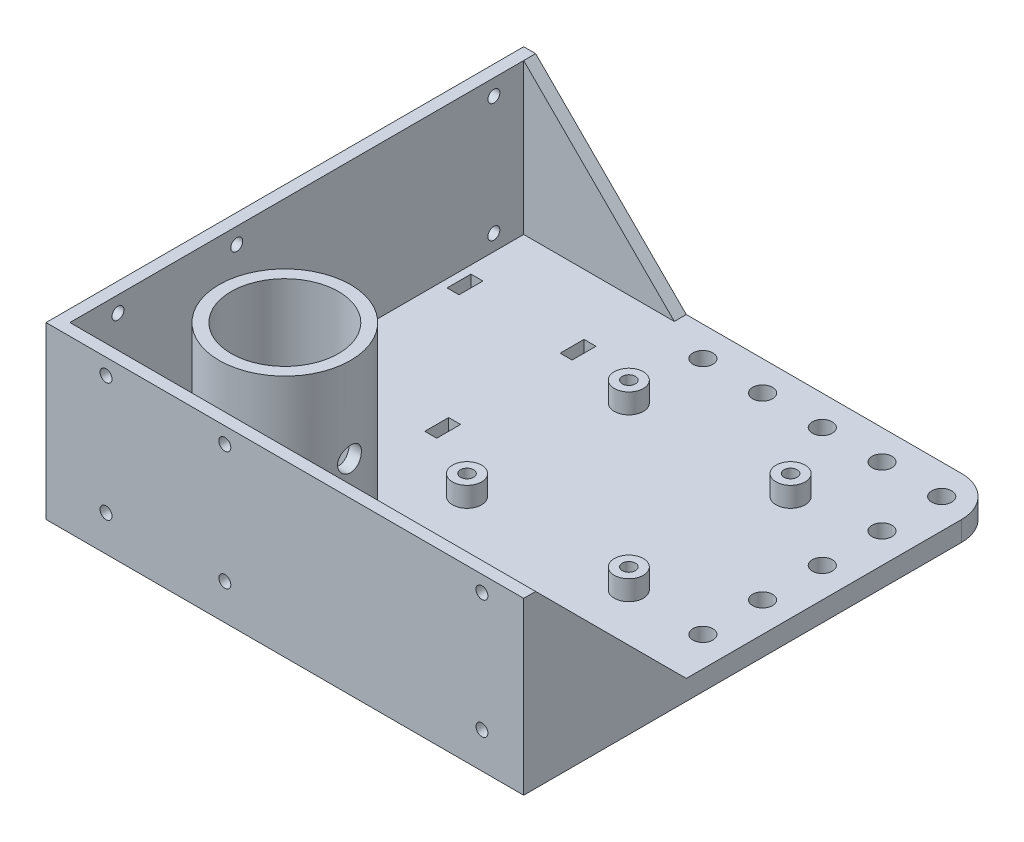
SolidWorks part; units mm, degrees
ref_plane "Front Plane" through (0, 0, 0) normal (0, 0, 1) x (1, 0, 0)
ref_plane "Top Plane" through (0, 0, 0) normal (0, 1, 0) x (1, 0, 0)
ref_plane "Right Plane" through (0, 0, 0) normal (1, 0, 0) x (0, 0, -1)
sketch "Sketch1" plane through (0, 0, 0) normal (0, 1, 0) x (1, 0, 0)
  line L0 (-30, -30) -> (90, 90) construction
  line L1 (-30, -30) -> (90, -30)
  line L2 (-30, -30) -> (-30, 90)
  line L3 (-30, 90) -> (90, 90)
  line L4 (90, -30) -> (90, 90)
  dimension "D1" = 120
  dimension "D2" = 30
extrude "Boss-Extrude1" add sketch "Sketch1" against normal blind 5
sketch "Sketch2" plane through (0, 0, 0) normal (0, 1, 0) x (1, 0, 0)
  line L0 (-30, 90) -> (-27, 90)
  line L1 (90, 90) -> (-30, 90) construction
  line L2 (-27, 90) -> (-27, -27)
  line L3 (-27, -27) -> (90, -27)
  line L4 (90, -30) -> (90, 90) construction
  line L5 (90, -27) -> (90, -30)
  line L6 (90, -30) -> (-30, -30)
  line L7 (-30, -30) -> (-30, 90)
  dimension "D1" = 3
extrude "Boss-Extrude2" add sketch "Sketch2" along normal blind 42.84 from surface at -5 starting at face at (30, -5, -30)
sketch "Sketch6" plane through (0, 0, 30) normal (0, 0, 1) x (1, 0, 0)
  line L0 (-14.92, 33.84) -> (14.92, 4) construction
  line L1 (14.92, 33.84) -> (-14.92, 4) construction
  line L3 (90, 37.84) -> (-30, 37.84) construction
  line L4 (90, 37.84) -> (90, 0) construction
  line L5 (90, 37.84) -> (90, 0) construction
  circle A0 centre (-14.92, 33.84) radius 1.5
  circle A1 centre (14.92, 33.84) radius 1.5
  circle A2 centre (14.92, 4) radius 1.5
  circle A3 centre (-14.92, 4) radius 1.5
  circle A4 centre (79.5, 33.84) radius 1.5
  circle A5 centre (79.5, 4) radius 1.5
  point P4 (0, 18.92)
  point P21 (90, 18.92)
  dimension "D3" = 3
  dimension "D1" = 42.2
  dimension "D2" = 45
  dimension "D4" = 64.58
extrude "Cut-Extrude1" cut sketch "Sketch6" against normal through all
ref_plane "Plane1" through (0, 0, 0) normal (-0.7071, 0, -0.7071) x (-0.7071, 0, 0.7071)
mirror "Mirror1" about plane through (0, 0, 0) normal (-0.7071, 0, -0.7071) of "Cut-Extrude1"
sketch "Sketch3" plane through (90, 0, 0) normal (1, 0, 0) x (0, 0, -1)
  line L0 (-27, 37.84) -> (-27, 0)
  line L1 (-27, 0) -> (10.84, 0)
  line L2 (-27, 0) -> (90, 0) construction
  line L3 (10.84, 0) -> (-27, 37.84)
extrude "Boss-Extrude3" add sketch "Sketch3" against normal blind 3
sketch "Sketch7" plane through (0, 0, 0) normal (0, 1, 0) x (1, 0, 0)
  circle A0 centre (0, 0) radius 13.5
  dimension "D1" = 27
extrude "Cut-Extrude2" cut sketch "Sketch7" against normal through all
sketch "Sketch8" plane through (0, 0, 0) normal (0, 1, 0) x (1, 0, 0)
  circle A0 centre (0, 0) radius 13.5 construction
  circle A1 centre (0, 0) radius 13.5
  circle A2 centre (0, 0) radius 16.5
  dimension "D1" = 3
extrude "Boss-Extrude5" add sketch "Sketch8" along normal through all
sketch "Sketch9" plane through (0, 0, 0) normal (1, 0, 0) x (0, 0, -1)
  line L0 (0, 37.84) -> (0, -5) construction
  line L1 (13.5, 37.84) -> (-13.5, 37.84) construction
  line L2 (-30, -5) -> (90, -5) construction
  circle A0 centre (0, 16.42) radius 3
  dimension "D1" = 6
extrude "Cut-Extrude3" cut sketch "Sketch9" along normal through all
sketch "Sketch10" plane through (0, 0, 0) normal (0, 1, 0) x (1, 0, 0)
  line L0 (37.75, 3.4) -> (65.75, -22) construction
  line L5 (31.75, 3.4) -> (37.75, 3.4)
  line L6 (31.75, 3.4) -> (31.75, 6.4)
  line L7 (31.75, 6.4) -> (37.75, 6.4)
  line L8 (37.75, 3.4) -> (37.75, 6.4)
  line L9 (71.75, 3.4) -> (65.75, 3.4)
  line L10 (71.75, 3.4) -> (71.75, 6.4)
  line L11 (71.75, 6.4) -> (65.75, 6.4)
  line L12 (65.75, 3.4) -> (65.75, 6.4)
  line L13 (71.75, -22) -> (65.75, -22)
  line L14 (71.75, -22) -> (71.75, -25)
  line L15 (71.75, -25) -> (65.75, -25)
  line L16 (65.75, -22) -> (65.75, -25)
  line L17 (31.75, -22) -> (37.75, -22)
  line L18 (31.75, -22) -> (31.75, -25)
  line L19 (31.75, -25) -> (37.75, -25)
  line L20 (37.75, -22) -> (37.75, -25)
  line L21 (21.75, 3.4) -> (81.75, 3.4) construction
  line L22 (21.75, 3.4) -> (21.75, -22) construction
  line L23 (21.75, -22) -> (81.75, -22) construction
  line L24 (81.75, 3.4) -> (81.75, -22) construction
  line L25 (-27, -27) -> (87, -27) construction
  line L27 (16.5, 0) -> (21.75, 0) construction
  line L28 (81.75, -9.3) -> (87, -9.3) construction
  line L29 (87, 10.84) -> (87, -27) construction
  line L30 (90, 90) -> (-30, -30) construction
  line L31 (90, 10.84) -> (90, 90) construction
  circle A0 centre (0, 0) radius 16.5 construction
  circle A1 centre (0, 0) radius 16.5 construction
  circle A2 centre (82.5, 82.5) radius 2.5
  circle A3 centre (82.5, 67.5) radius 2.5
  circle A4 centre (82.5, 52.5) radius 2.5
  circle A5 centre (82.5, 37.5) radius 2.5
  circle A6 centre (82.5, 22.5) radius 2.5
  point P20 (51.75, -9.3)
  point P21 (51.75, 3.4)
  dimension "D8" = 5
  dimension "D1" = 3
  dimension "D2" = 6
  dimension "D3" = 10
  dimension "D4" = 60
  dimension "D5" = 2
  dimension "D6" = 7.5
  dimension "D7" = 25.4
  dimension "D9" = 15
extrude "Cut-Extrude4" cut sketch "Sketch10" against normal through all
mirror "Mirror2" about plane through (0, 0, 0) normal (-0.7071, 0, -0.7071) of "Cut-Extrude4", "Boss-Extrude3", "Cut-Extrude3"
fillet "Fillet1" radius 10 1 edges at (90, -2.5, -90)
sketch "Sketch11" plane through (0, 0, 0) normal (0, 1, 0) x (1, 0, 0)
  line L0 (34.75, 6.4) -> (34.75, 17.8) construction
  line L1 (17.8, 17.8) -> (68.6, 17.8) construction
  line L2 (17.8, 17.8) -> (17.8, 68.6) construction
  line L3 (17.8, 68.6) -> (68.6, 68.6) construction
  line L4 (68.6, 17.8) -> (68.6, 68.6) construction
  line L5 (22.88, 22.88) -> (22.88, 63.52) construction
  line L6 (22.88, 63.52) -> (63.52, 63.52) construction
  line L7 (37.75, 6.4) -> (31.75, 6.4) construction
  line L8 (6.4, 31.75) -> (17.8, 31.75) construction
  line L9 (37.5, 80) -> (37.5, 68.6) construction
  line L10 (80, 37.5) -> (68.6, 37.5) construction
  line L19 (63.52, 22.88) -> (63.52, 63.52) construction
  line L20 (22.88, 22.88) -> (63.52, 22.88) construction
  circle A0 centre (22.88, 63.52) radius 1.65
  circle A1 centre (37.5, 82.5) radius 2.5 construction
  circle A2 centre (82.5, 37.5) radius 2.5 construction
  circle A4 centre (63.52, 63.52) radius 1.65
  circle A5 centre (63.52, 22.88) radius 1.65
  circle A6 centre (22.88, 22.88) radius 1.65
  dimension "D3" = 3.3
  dimension "D1" = 50.8
  dimension "D2" = 5.08
extrude "Cut-Extrude5" cut sketch "Sketch11" against normal through all
sketch "Sketch12" plane through (0, 0, 0) normal (0, 1, 0) x (1, 0, 0)
  circle A0 centre (22.88, 22.88) radius 1.65 construction
  circle A1 centre (63.52, 22.88) radius 1.65 construction
  circle A2 centre (63.52, 63.52) radius 1.65 construction
  circle A3 centre (22.88, 63.52) radius 1.65 construction
  circle A4 centre (22.88, 22.88) radius 1.65
  circle A5 centre (63.52, 22.88) radius 1.65
  circle A6 centre (63.52, 63.52) radius 1.65
  circle A7 centre (22.88, 63.52) radius 1.65
  circle A8 centre (22.88, 63.52) radius 3.65
  circle A9 centre (63.52, 63.52) radius 3.65
  circle A10 centre (63.52, 22.88) radius 3.65
  circle A11 centre (22.88, 22.88) radius 3.65
  dimension "D1" = 2
extrude "Boss-Extrude6" add sketch "Sketch12" along normal blind 5
chamfer "Chamfer1" distance 2.5 angle 45 4 edges at (63.52, -5, -21.23) (63.52, -5, -61.87) (22.88, -5, -61.87) (22.88, -5, -21.23)
